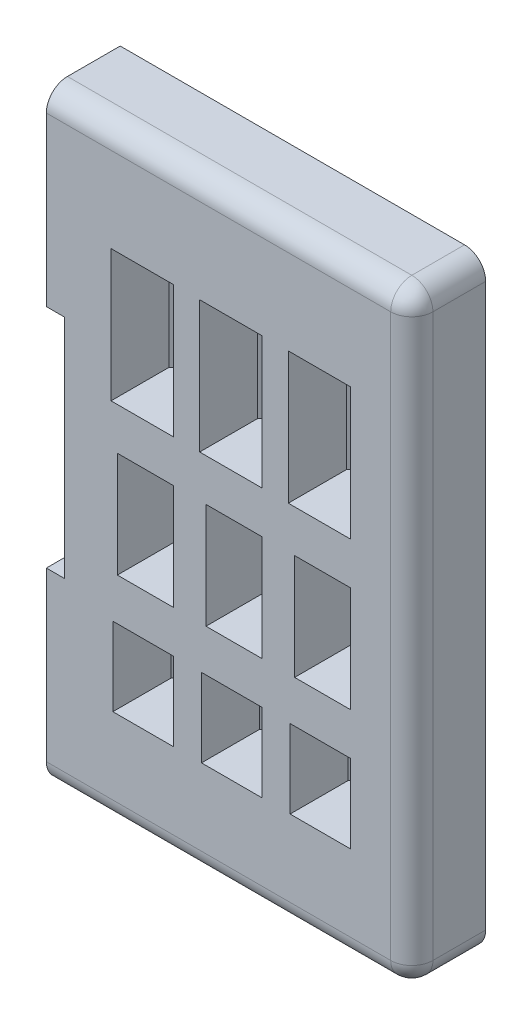
SolidWorks part; units mm, degrees
ref_plane "Alzado" through (0, 0, 0) normal (0, 0, 1) x (1, 0, 0)
ref_plane "Planta" through (0, 0, 0) normal (0, 1, 0) x (1, 0, 0)
ref_plane "Vista lateral" through (0, 0, 0) normal (1, 0, 0) x (0, 0, -1)
sketch "Croquis1" plane through (0, 0, 0) normal (0, 0, 1) x (1, 0, 0)
  line L80 (30.4082, 43.7605) -> (24.5082, 43.7605)
  line L81 (30.4082, 43.7605) -> (30.4082, 31.2605)
  line L82 (30.4082, 31.2605) -> (24.5082, 31.2605)
  line L83 (24.5082, 43.7605) -> (24.5082, 31.2605)
  line L84 (30.4082, 27.2605) -> (25.1082, 27.2605)
  line L85 (30.4082, 27.2605) -> (30.4082, 17.2605)
  line L86 (30.4082, 17.2605) -> (25.1082, 17.2605)
  line L87 (25.1082, 27.2605) -> (25.1082, 17.2605)
  line L88 (30.4082, 13.2605) -> (24.6805, 13.2605)
  line L89 (3.3192, 26.4922) -> (3.3192, 23.9078)
  line L90 (3.3192, 23.9078) -> (3.3192, 14.4717)
  line L91 (3.3192, 35.9283) -> (3.3192, 26.4922)
  line L92 (3.3192, 1.2771) -> (6.3251, 1.2771)
  line L93 (3.3192, 14.4717) -> (3.3192, 1.2771)
  line L94 (3.3192, 49.1229) -> (3.3192, 35.9283)
  line L95 (6.3251, 49.1229) -> (3.3192, 49.1229)
  line L96 (6.3251, 1.2771) -> (31.2135, 1.2771)
  line L97 (31.2135, 49.1229) -> (6.3251, 49.1229)
  line L98 (34.2135, 4.2771) -> (34.2135, 46.1229)
  line L106 (6.3251, 1.2771) -> (31.2135, 1.2771)
  line L107 (31.2135, 49.1229) -> (6.3251, 49.1229)
  line L108 (34.2135, 4.2771) -> (34.2135, 46.1229)
  line L109 (30.4082, 13.2605) -> (30.4082, 5.831)
  line L110 (30.4082, 5.831) -> (24.6805, 5.831)
  line L111 (24.6805, 13.2605) -> (24.6805, 5.831)
  line L112 (22.0082, 43.7605) -> (16.1082, 43.7605)
  line L113 (22.0082, 43.7605) -> (22.0082, 31.2605)
  line L114 (22.0082, 31.2605) -> (16.1082, 31.2605)
  line L115 (16.1082, 43.7605) -> (16.1082, 31.2605)
  line L116 (22.0082, 27.2605) -> (16.7082, 27.2605)
  line L117 (22.0082, 27.2605) -> (22.0082, 17.2605)
  line L118 (22.0082, 17.2605) -> (16.7082, 17.2605)
  line L119 (16.7082, 27.2605) -> (16.7082, 17.2605)
  line L120 (22.0082, 13.2605) -> (16.2805, 13.2605)
  line L121 (22.0082, 13.2605) -> (22.0082, 5.831)
  line L122 (22.0082, 5.831) -> (16.2805, 5.831)
  line L123 (16.2805, 13.2605) -> (16.2805, 5.831)
  line L124 (13.6082, 43.7605) -> (7.7082, 43.7605)
  line L125 (13.6082, 43.7605) -> (13.6082, 31.2605)
  line L126 (13.6082, 31.2605) -> (7.7082, 31.2605)
  line L127 (7.7082, 43.7605) -> (7.7082, 31.2605)
  line L128 (13.6082, 27.2605) -> (8.3082, 27.2605)
  line L129 (13.6082, 27.2605) -> (13.6082, 17.2605)
  line L130 (13.6082, 17.2605) -> (8.3082, 17.2605)
  line L131 (8.3082, 27.2605) -> (8.3082, 17.2605)
  line L132 (13.6082, 13.2605) -> (7.8805, 13.2605)
  line L133 (13.6082, 13.2605) -> (13.6082, 5.831)
  line L134 (13.6082, 5.831) -> (7.8805, 5.831)
  line L135 (7.8805, 13.2605) -> (7.8805, 5.831)
  line L145 (6.3251, 49.1229) -> (6.3251, 35.9283)
  line L146 (5.3326, 35.9283) -> (7.0041, 35.9283) construction
  line L147 (6.3251, 35.9283) -> (7.0041, 35.9283)
  line L148 (7.0041, 35.9283) -> (7.0041, 14.4717) construction
  line L149 (7.0041, 35.9283) -> (7.0041, 14.4717)
  line L150 (7.0041, 14.4717) -> (6.3251, 14.4717)
  line L151 (7.0041, 14.4717) -> (5.3326, 14.4717) construction
  line L152 (6.3251, 14.4717) -> (6.3251, 1.2771)
  arc A29 (31.2135, 1.2771) -> (34.2135, 4.2771) centre (31.2135, 4.2771) ccw
  arc A30 (34.2135, 46.1229) -> (31.2135, 49.1229) centre (31.2135, 46.1229) ccw
  arc A31 (31.2135, 1.2771) -> (34.2135, 4.2771) centre (31.2135, 4.2771) ccw
  arc A32 (34.2135, 46.1229) -> (31.2135, 49.1229) centre (31.2135, 46.1229) ccw
  dimension "D1" = 0
extrude "Saliente-Extruir1" add sketch "Croquis1" against normal blind 1
sketch "Croquis2" plane through (0, 0, 0) normal (0, 0, 1) x (1, 0, 0)
  line L8 (1.5763, -3.4208) -> (1.5763, 14.4717) construction
  line L9 (36.2135, 53.82) -> (1.5763, 53.82)
  line L10 (36.2135, 53.82) -> (36.2135, -3.4208)
  line L11 (36.2135, -3.4208) -> (1.5763, -3.4208)
  line L12 (1.5763, 53.82) -> (1.5763, 35.9283)
  line L13 (3.3192, 35.9283) -> (1.5763, 35.9283)
  line L14 (3.3192, 35.9283) -> (3.3192, 14.4717)
  line L15 (3.3192, 14.4717) -> (1.5763, 14.4717)
  line L17 (1.5763, 14.4717) -> (1.5763, -3.4208)
  line L19 (30.4082, 43.7605) -> (24.5082, 43.7605)
  line L20 (30.4082, 43.7605) -> (30.4082, 31.2605)
  line L21 (30.4082, 31.2605) -> (24.5082, 31.2605)
  line L22 (24.5082, 43.7605) -> (24.5082, 31.2605)
  line L23 (30.4082, 27.2605) -> (25.1082, 27.2605)
  line L24 (30.4082, 27.2605) -> (30.4082, 17.2605)
  line L25 (30.4082, 17.2605) -> (25.1082, 17.2605)
  line L26 (25.1082, 27.2605) -> (25.1082, 17.2605)
  line L27 (30.4082, 13.2605) -> (24.6805, 13.2605)
  line L28 (30.4082, 13.2605) -> (30.4082, 5.831)
  line L29 (30.4082, 5.831) -> (24.6805, 5.831)
  line L30 (24.6805, 13.2605) -> (24.6805, 5.831)
  line L31 (22.0082, 13.2605) -> (16.2805, 13.2605)
  line L32 (22.0082, 13.2605) -> (22.0082, 5.831)
  line L33 (22.0082, 5.831) -> (16.2805, 5.831)
  line L34 (16.2805, 13.2605) -> (16.2805, 5.831)
  line L35 (22.0082, 27.2605) -> (16.7082, 27.2605)
  line L36 (22.0082, 27.2605) -> (22.0082, 17.2605)
  line L37 (22.0082, 17.2605) -> (16.7082, 17.2605)
  line L38 (16.7082, 27.2605) -> (16.7082, 17.2605)
  line L39 (22.0082, 43.7605) -> (16.1082, 43.7605)
  line L40 (22.0082, 43.7605) -> (22.0082, 31.2605)
  line L41 (22.0082, 31.2605) -> (16.1082, 31.2605)
  line L42 (16.1082, 43.7605) -> (16.1082, 31.2605)
  line L43 (13.6082, 43.7605) -> (7.7082, 43.7605)
  line L44 (13.6082, 43.7605) -> (13.6082, 31.2605)
  line L45 (13.6082, 31.2605) -> (7.7082, 31.2605)
  line L46 (7.7082, 43.7605) -> (7.7082, 31.2605)
  line L47 (13.6082, 27.2605) -> (8.3082, 27.2605)
  line L48 (13.6082, 27.2605) -> (13.6082, 17.2605)
  line L49 (13.6082, 17.2605) -> (8.3082, 17.2605)
  line L50 (8.3082, 27.2605) -> (8.3082, 17.2605)
  line L51 (13.6082, 13.2605) -> (7.8805, 13.2605)
  line L52 (13.6082, 13.2605) -> (13.6082, 5.831)
  line L53 (13.6082, 5.831) -> (7.8805, 5.831)
  line L54 (7.8805, 13.2605) -> (7.8805, 5.831)
extrude "Saliente-Extruir2" add sketch "Croquis2" along normal blind 7
sketch "Croquis3" plane through (0, 0, -1) normal (0, 0, -1) x (-1, 0, 0)
  line L1 (-30.4082, 5.831) -> (-29.2082, 5.831)
  line L2 (-30.4082, 5.831) -> (-30.4082, 13.2605)
  line L3 (-30.4082, 13.2605) -> (-29.2082, 13.2605)
  line L4 (-29.2082, 5.831) -> (-29.2082, 13.2605)
  line L5 (-22.0082, 5.831) -> (-20.8082, 5.831)
  line L6 (-24.6805, 5.831) -> (-25.8805, 5.831)
  line L7 (-24.6805, 5.831) -> (-24.6805, 13.2605)
  line L8 (-24.6805, 13.2605) -> (-25.8805, 13.2605)
  line L9 (-25.8805, 5.831) -> (-25.8805, 13.2605)
  line L10 (-22.0082, 5.831) -> (-22.0082, 13.2605)
  line L11 (-22.0082, 13.2605) -> (-20.8082, 13.2605)
  line L12 (-20.8082, 5.831) -> (-20.8082, 13.2605)
  line L13 (-16.2805, 5.831) -> (-17.4805, 5.831)
  line L14 (-16.2805, 5.831) -> (-16.2805, 13.2605)
  line L15 (-16.2805, 13.2605) -> (-17.4805, 13.2605)
  line L16 (-17.4805, 5.831) -> (-17.4805, 13.2605)
  line L17 (-13.6082, 5.831) -> (-12.4082, 5.831)
  line L18 (-13.6082, 5.831) -> (-13.6082, 13.2605)
  line L19 (-13.6082, 13.2605) -> (-12.4082, 13.2605)
  line L20 (-12.4082, 5.831) -> (-12.4082, 13.2605)
  line L21 (-7.8805, 5.831) -> (-9.0805, 5.831)
  line L22 (-7.8805, 5.831) -> (-7.8805, 13.2605)
  line L23 (-7.8805, 13.2605) -> (-9.0805, 13.2605)
  line L24 (-9.0805, 5.831) -> (-9.0805, 13.2605)
  line L26 (-30.4082, 17.2605) -> (-29.2082, 17.2605)
  line L27 (-30.4082, 17.2605) -> (-30.4082, 27.2605)
  line L28 (-30.4082, 27.2605) -> (-29.2082, 27.2605)
  line L29 (-29.2082, 17.2605) -> (-29.2082, 27.2605)
  line L30 (-22.0082, 17.2605) -> (-20.8082, 17.2605)
  line L31 (-25.1082, 17.2605) -> (-26.3082, 17.2605)
  line L32 (-25.1082, 17.2605) -> (-25.1082, 27.2605)
  line L33 (-25.1082, 27.2605) -> (-26.3082, 27.2605)
  line L34 (-26.3082, 17.2605) -> (-26.3082, 27.2605)
  line L35 (-22.0082, 17.2605) -> (-22.0082, 27.2605)
  line L36 (-22.0082, 27.2605) -> (-20.8082, 27.2605)
  line L37 (-20.8082, 17.2605) -> (-20.8082, 27.2605)
  line L38 (-16.7082, 17.2605) -> (-17.9082, 17.2605)
  line L39 (-16.7082, 17.2605) -> (-16.7082, 27.2605)
  line L40 (-16.7082, 27.2605) -> (-17.9082, 27.2605)
  line L41 (-17.9082, 17.2605) -> (-17.9082, 27.2605)
  line L42 (-13.6082, 17.2605) -> (-12.4082, 17.2605)
  line L43 (-13.6082, 17.2605) -> (-13.6082, 27.2605)
  line L44 (-13.6082, 27.2605) -> (-12.4082, 27.2605)
  line L45 (-12.4082, 17.2605) -> (-12.4082, 27.2605)
  line L46 (-8.3082, 17.2605) -> (-9.5082, 17.2605)
  line L47 (-8.3082, 17.2605) -> (-8.3082, 27.2605)
  line L48 (-8.3082, 27.2605) -> (-9.5082, 27.2605)
  line L49 (-9.5082, 17.2605) -> (-9.5082, 27.2605)
  line L51 (-30.4082, 31.2605) -> (-29.2082, 31.2605)
  line L52 (-30.4082, 31.2605) -> (-30.4082, 43.7605)
  line L53 (-30.4082, 43.7605) -> (-29.2082, 43.7605)
  line L54 (-29.2082, 31.2605) -> (-29.2082, 43.7605)
  line L55 (-24.5082, 31.2605) -> (-25.7082, 31.2605)
  line L56 (-24.5082, 31.2605) -> (-24.5082, 43.7605)
  line L57 (-24.5082, 43.7605) -> (-25.7082, 43.7605)
  line L58 (-25.7082, 31.2605) -> (-25.7082, 43.7605)
  line L59 (-22.0082, 31.2605) -> (-20.8082, 31.2605)
  line L60 (-22.0082, 31.2605) -> (-22.0082, 43.7605)
  line L61 (-22.0082, 43.7605) -> (-20.8082, 43.7605)
  line L62 (-20.8082, 31.2605) -> (-20.8082, 43.7605)
  line L63 (-16.1082, 31.2605) -> (-17.3082, 31.2605)
  line L64 (-16.1082, 31.2605) -> (-16.1082, 43.7605)
  line L65 (-16.1082, 43.7605) -> (-17.3082, 43.7605)
  line L66 (-17.3082, 31.2605) -> (-17.3082, 43.7605)
  line L67 (-13.6082, 31.2605) -> (-12.4082, 31.2605)
  line L68 (-13.6082, 31.2605) -> (-13.6082, 43.7605)
  line L69 (-13.6082, 43.7605) -> (-12.4082, 43.7605)
  line L70 (-12.4082, 31.2605) -> (-12.4082, 43.7605)
  line L71 (-7.7082, 31.2605) -> (-8.9082, 31.2605)
  line L72 (-7.7082, 31.2605) -> (-7.7082, 43.7605)
  line L73 (-7.7082, 43.7605) -> (-8.9082, 43.7605)
  line L74 (-8.9082, 31.2605) -> (-8.9082, 43.7605)
  point P84 (-30.4082, 43.7605)
extrude "Saliente-Extruir3" add sketch "Croquis3" against normal blind 1.5
chamfer "Chaflán1" distance 1 angle 45 18 edges at (24.6805, 9.5457, 0.5) (16.2805, 9.5457, 0.5) (7.8805, 9.5457, 0.5) (30.4082, 9.5457, 0.5) (22.0082, 9.5457, 0.5) (13.6082, 9.5457, 0.5) (13.6082, 22.2605, 0.5) (13.6082, 37.5105, 0.5) (22.0082, 37.5105, 0.5) (22.0082, 22.2605, 0.5) (30.4082, 22.2605, 0.5) (25.1082, 22.2605, 0.5) (8.3082, 22.2605, 0.5) (7.7082, 37.5105, 0.5) (16.1082, 37.5105, 0.5) (24.5082, 37.5105, 0.5) (30.4082, 37.5105, 0.5) (16.7082, 22.2605, 0.5)
fillet "Redondeo1" radius 2 5 edges at (36.2135, -3.4208, 3.5) (36.2135, 53.82, 3.5) (18.8949, 53.82, 7) (18.8949, -3.4208, 7) (36.2135, 25.1996, 7)
